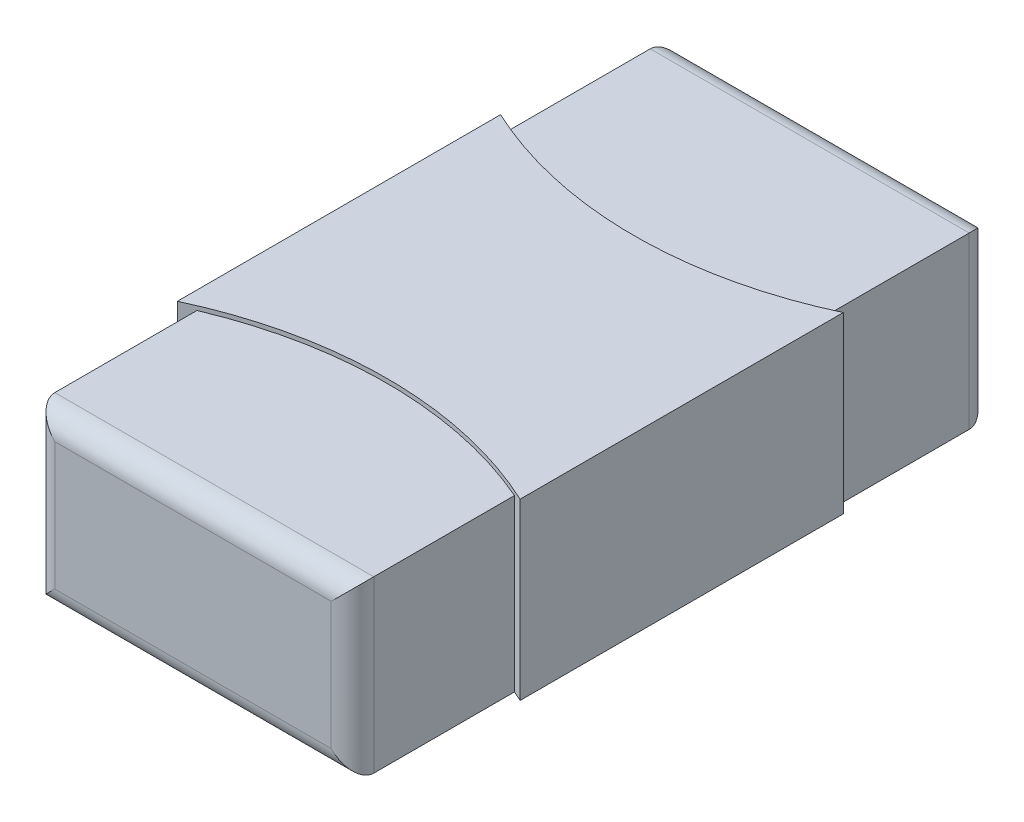
SolidWorks part; units mm, degrees
ref_plane "Plan de face" through (0, 0, 0) normal (0, 0, 1) x (1, 0, 0)
ref_plane "Plan de dessus" through (0, 0, 0) normal (0, 1, 0) x (1, 0, 0)
ref_plane "Plan de droite" through (0, 0, 0) normal (1, 0, 0) x (0, 0, -1)
sketch "Esquisse1" plane through (0, 0, 0) normal (0, 1, 0) x (1, 0, 0)
  line L1 (0.75, -1.5) -> (-0.75, -1.5)
  line L2 (0.75, -1.5) -> (0.75, 1.5)
  line L3 (0.75, 1.5) -> (-0.75, 1.5)
  line L4 (-0.75, -1.5) -> (-0.75, 1.5)
  line L5 (0.75, -1.5) -> (-0.75, 1.5) construction
  line L6 (0.75, 1.5) -> (-0.75, -1.5) construction
  point P0 (0, 0)
  dimension "D1" = 3
  dimension "D2" = 1.5
extrude "Boss.-Extru.1" add sketch "Esquisse1" along normal blind 0.8
fillet "Congé1" radius 0.1 8 edges at (0.75, 0.4, -1.5) (0, 0.8, -1.5) (-0.75, 0.4, -1.5) (0, 0, -1.5) (-0.75, 0.4, 1.5) (0, 0.8, 1.5) (0.75, 0.4, 1.5) (0, 0, 1.5)
sketch "Esquisse2" plane through (0, 0.8, 0) normal (0, 1, 0) x (1, 0, 0)
  line L0 (-0.9, 0) -> (0.9, 0) construction
  line L1 (-0.8137, -0.7599) -> (-0.8137, 0.7599)
  line L2 (0.798, 0.7599) -> (0.798, -0.7599)
  arc A0 (-0.8137, -0.7599) -> (0.798, -0.7599) centre (-0.0079, -2.4849) cw
  arc A1 (-0.8137, 0.7599) -> (0.798, 0.7599) centre (-0.0079, 2.4849) ccw
extrude "Boss.-Extru.2" add sketch "Esquisse2" along normal blind 0.02 and the other way blind 0.8
